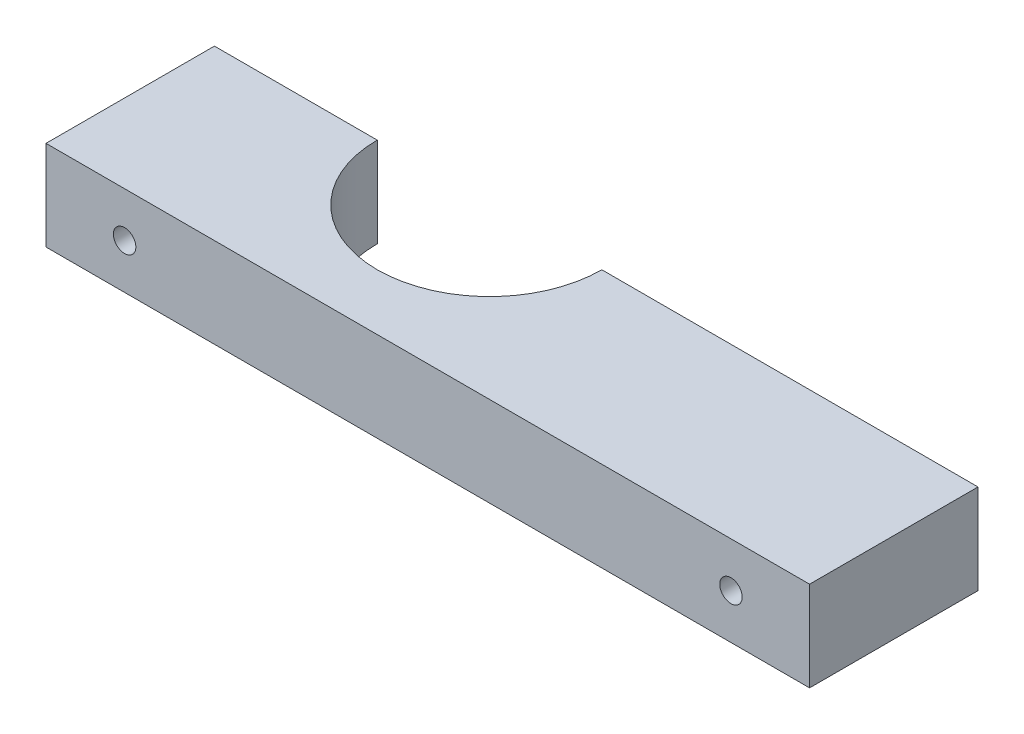
SolidWorks part; units mm, degrees
ref_plane "Front Plane" through (0, 0, 0) normal (0, 0, 1) x (1, 0, 0)
ref_plane "Top Plane" through (0, 0, 0) normal (0, 1, 0) x (1, 0, 0)
ref_plane "Right Plane" through (0, 0, 0) normal (1, 0, 0) x (0, 0, -1)
sketch "Sketch1" plane through (0, 0, 0) normal (0, 1, 0) x (1, 0, 0)
  line L0 (2.6493, -0.3406) -> (36.1493, -0.3406)
  line L1 (-31.8507, -0.3406) -> (-17.3507, -0.3406)
  line L2 (-31.8507, -0.3406) -> (-31.8507, -15.3406)
  line L3 (-31.8507, -15.3406) -> (36.1493, -15.3406)
  line L4 (36.1493, -0.3406) -> (36.1493, -15.3406)
  arc A0 (-17.3507, -0.3406) -> (2.6493, -0.3406) centre (-7.3507, -0.3406) ccw
  dimension "D1" = 24.5
  dimension "D3" = 15
  dimension "D2" = 68
extrude "Boss-Extrude1" add sketch "Sketch1" along normal blind 8
sketch "Sketch2" plane through (0, 0, 0) normal (0, 0, 1) x (1, 0, 0)
  line L0 (-31.8507, 4) -> (36.1493, 4) construction
  line L1 (-31.8507, 8) -> (-31.8507, 0) construction
  line L2 (36.1493, 8) -> (36.1493, 0) construction
  circle A0 centre (-24.8507, 4) radius 1
  circle A1 centre (29.1493, 4) radius 1
  dimension "D1" = 2
  dimension "D2" = 2
  dimension "D3" = 7
  dimension "D4" = 7
extrude "Cut-Extrude1" cut sketch "Sketch2" along normal through all
